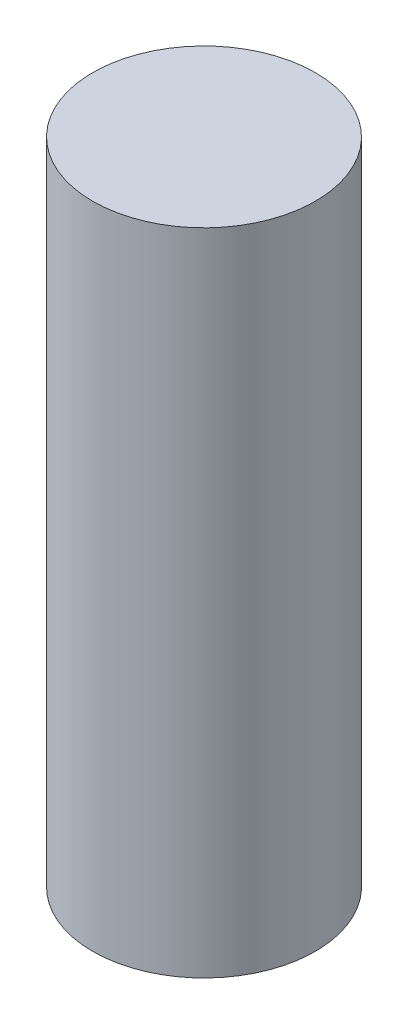
SolidWorks part; units mm, degrees
ref_plane "Front Plane" through (0, 0, 0) normal (0, 0, 1) x (1, 0, 0)
ref_plane "Top Plane" through (0, 0, 0) normal (0, 1, 0) x (1, 0, 0)
ref_plane "Right Plane" through (0, 0, 0) normal (1, 0, 0) x (0, 0, -1)
sketch "Sketch1" plane through (0, 0, 0) normal (0, 1, 0) x (1, 0, 0)
  circle A0 centre (0, 0) radius 6
  dimension "D1" = 12
extrude "Boss-Extrude1" add sketch "Sketch1" along normal blind 35
